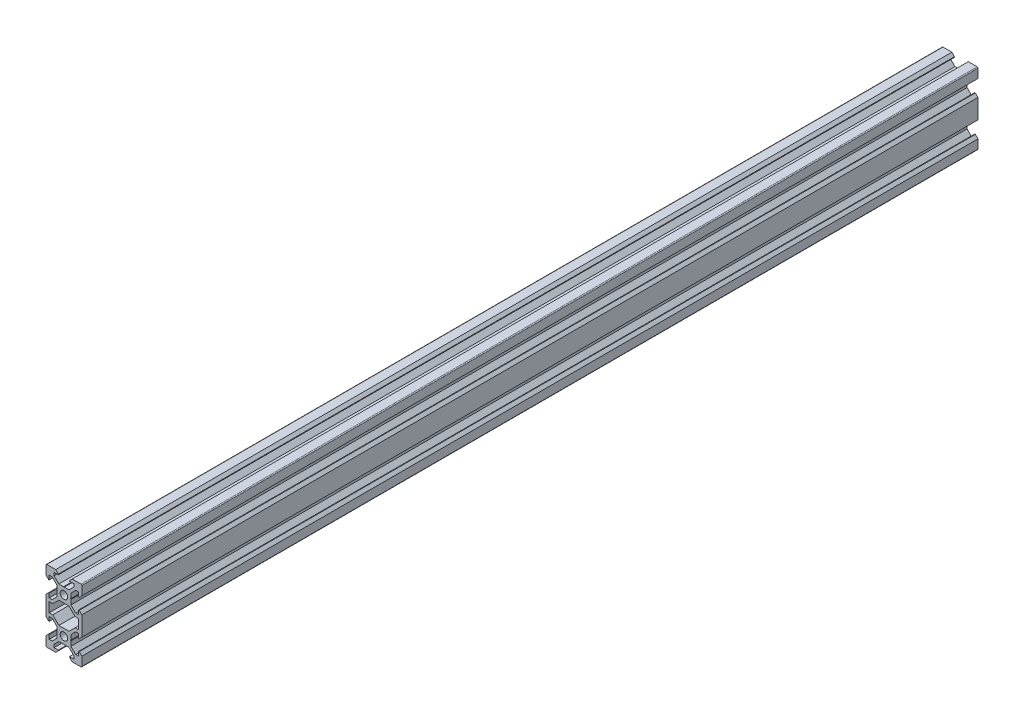
SolidWorks part; units mm, degrees
ref_plane "Front Plane" through (0, 0, 0) normal (0, 0, 1) x (1, 0, 0)
ref_plane "Top Plane" through (0, 0, 0) normal (0, 1, 0) x (1, 0, 0)
ref_plane "Right Plane" through (0, 0, 0) normal (1, 0, 0) x (0, 0, -1)
ref_plane "Plane4" through (0, 0, 0) normal (0, 0, -1) x (-1, 0, 0)
sketch "Sketch1" plane through (0, 0, 0) normal (0, 0, -1) x (-1, 0, 0)
  line L0 (6.2393, -2.7) -> (2.8393, -6.1)
  line L1 (2.8393, -6.1) -> (-2.8393, -6.1)
  line L2 (-2.8393, -6.1) -> (-6.2393, -2.7)
  line L3 (-6.2393, -2.7) -> (-8.2, -2.7)
  line L4 (-8.2, -2.7) -> (-8.2, 2.7)
  line L5 (-8.2, 2.7) -> (-6.2393, 2.7)
  line L6 (-6.2393, 2.7) -> (-2.8393, 6.1)
  line L7 (-2.8393, 6.1) -> (2.8393, 6.1)
  line L8 (2.8393, 6.1) -> (6.2393, 2.7)
  line L9 (6.2393, 2.7) -> (8.2, 2.7)
  line L10 (8.2, 2.7) -> (8.2, -2.7)
  line L11 (8.2, -2.7) -> (6.2393, -2.7)
  line L12 (-3.9, 9.79) -> (-3.9, 7.1607)
  line L13 (-3.9, 7.1607) -> (-6.5607, 4.5)
  line L14 (-6.5607, 4.5) -> (-8.2, 4.5)
  line L15 (-8.2, 4.5) -> (-8.2, 6.875)
  line L16 (-8.2, 6.875) -> (-8.545, 6.875)
  line L17 (-8.545, 6.875) -> (-10, 5.42)
  line L18 (-10, 5.42) -> (-10, -5.42)
  line L19 (-10, -5.42) -> (-8.545, -6.875)
  line L20 (-8.545, -6.875) -> (-8.2, -6.875)
  line L21 (-8.2, -6.875) -> (-8.2, -4.5)
  line L22 (-8.2, -4.5) -> (-6.5607, -4.5)
  line L23 (-6.5607, -4.5) -> (-3.9, -7.1607)
  line L24 (-3.9, -7.1607) -> (-3.9, -9.79)
  line L25 (-3.9, -9.79) -> (-3.69, -10)
  line L26 (-3.69, -10) -> (-3.9, -10.21)
  line L27 (-3.9, -10.21) -> (-3.9, -12.8393)
  line L28 (-3.9, -12.8393) -> (-6.5607, -15.5)
  line L29 (-6.5607, -15.5) -> (-8.2, -15.5)
  line L30 (-8.2, -15.5) -> (-8.2, -13.125)
  line L31 (-8.2, -13.125) -> (-8.545, -13.125)
  line L32 (-8.545, -13.125) -> (-10, -14.58)
  line L33 (-10, -14.58) -> (-10, -19.5)
  line L34 (-9.5, -20) -> (-4.58, -20)
  line L35 (-4.58, -20) -> (-3.125, -18.545)
  line L36 (-3.125, -18.545) -> (-3.125, -18.2)
  line L37 (-3.125, -18.2) -> (-5.5, -18.2)
  line L38 (-5.5, -18.2) -> (-5.5, -16.5607)
  line L39 (-5.5, -16.5607) -> (-2.8393, -13.9)
  line L40 (-2.8393, -13.9) -> (-0.21, -13.9)
  line L41 (-0.21, -13.9) -> (0, -13.69)
  line L42 (0, -13.69) -> (0.21, -13.9)
  line L43 (0.21, -13.9) -> (2.8393, -13.9)
  line L44 (2.8393, -13.9) -> (5.5, -16.5607)
  line L45 (5.5, -16.5607) -> (5.5, -18.2)
  line L46 (5.5, -18.2) -> (3.125, -18.2)
  line L47 (3.125, -18.2) -> (3.125, -18.545)
  line L48 (3.125, -18.545) -> (4.58, -20)
  line L49 (4.58, -20) -> (9.5, -20)
  line L50 (10, -19.5) -> (10, -14.58)
  line L51 (10, -14.58) -> (8.545, -13.125)
  line L52 (8.545, -13.125) -> (8.2, -13.125)
  line L53 (8.2, -13.125) -> (8.2, -15.5)
  line L54 (8.2, -15.5) -> (6.5607, -15.5)
  line L55 (6.5607, -15.5) -> (3.9, -12.8393)
  line L56 (3.9, -12.8393) -> (3.9, -10.21)
  line L57 (3.9, -10.21) -> (3.69, -10)
  line L58 (3.69, -10) -> (3.9, -9.79)
  line L59 (3.9, -9.79) -> (3.9, -7.1607)
  line L60 (3.9, -7.1607) -> (6.5607, -4.5)
  line L61 (6.5607, -4.5) -> (8.2, -4.5)
  line L62 (8.2, -4.5) -> (8.2, -6.875)
  line L63 (8.2, -6.875) -> (8.545, -6.875)
  line L64 (8.545, -6.875) -> (10, -5.42)
  line L65 (10, -5.42) -> (10, 5.42)
  line L66 (10, 5.42) -> (8.545, 6.875)
  line L67 (8.545, 6.875) -> (8.2, 6.875)
  line L68 (8.2, 6.875) -> (8.2, 4.5)
  line L69 (8.2, 4.5) -> (6.5607, 4.5)
  line L70 (6.5607, 4.5) -> (3.9, 7.1607)
  line L71 (3.9, 7.1607) -> (3.9, 9.79)
  line L72 (3.9, 9.79) -> (3.69, 10)
  line L73 (3.69, 10) -> (3.9, 10.21)
  line L74 (3.9, 10.21) -> (3.9, 12.8393)
  line L75 (3.9, 12.8393) -> (6.5607, 15.5)
  line L76 (6.5607, 15.5) -> (8.2, 15.5)
  line L77 (8.2, 15.5) -> (8.2, 13.125)
  line L78 (8.2, 13.125) -> (8.545, 13.125)
  line L79 (8.545, 13.125) -> (10, 14.58)
  line L80 (10, 14.58) -> (10, 19.5)
  line L81 (9.5, 20) -> (4.58, 20)
  line L82 (4.58, 20) -> (3.125, 18.545)
  line L83 (3.125, 18.545) -> (3.125, 18.2)
  line L84 (3.125, 18.2) -> (5.5, 18.2)
  line L85 (5.5, 18.2) -> (5.5, 16.5607)
  line L86 (5.5, 16.5607) -> (2.8393, 13.9)
  line L87 (2.8393, 13.9) -> (0.21, 13.9)
  line L88 (0.21, 13.9) -> (0, 13.69)
  line L89 (0, 13.69) -> (-0.21, 13.9)
  line L90 (-0.21, 13.9) -> (-2.8393, 13.9)
  line L91 (-2.8393, 13.9) -> (-5.5, 16.5607)
  line L92 (-5.5, 16.5607) -> (-5.5, 18.2)
  line L93 (-5.5, 18.2) -> (-3.125, 18.2)
  line L94 (-3.125, 18.2) -> (-3.125, 18.545)
  line L95 (-3.125, 18.545) -> (-4.58, 20)
  line L96 (-4.58, 20) -> (-9.5, 20)
  line L97 (-10, 19.5) -> (-10, 14.58)
  line L98 (-10, 14.58) -> (-8.545, 13.125)
  line L99 (-8.545, 13.125) -> (-8.2, 13.125)
  line L100 (-8.2, 13.125) -> (-8.2, 15.5)
  line L101 (-8.2, 15.5) -> (-6.5607, 15.5)
  line L102 (-6.5607, 15.5) -> (-3.9, 12.8393)
  line L103 (-3.9, 12.8393) -> (-3.9, 10.21)
  line L104 (-3.9, 10.21) -> (-3.69, 10)
  line L105 (-3.69, 10) -> (-3.9, 9.79)
  circle A0 centre (0, 10) radius 2.1
  circle A1 centre (0, -10) radius 2.1
  arc A2 (-10, -19.5) -> (-9.5, -20) centre (-9.5, -19.5) ccw
  arc A3 (9.5, -20) -> (10, -19.5) centre (9.5, -19.5) ccw
  arc A4 (10, 19.5) -> (9.5, 20) centre (9.5, 19.5) ccw
  arc A5 (-9.5, 20) -> (-10, 19.5) centre (-9.5, 19.5) ccw
extrude "Boss-Extrude1" add sketch "Sketch1" against normal blind 500
